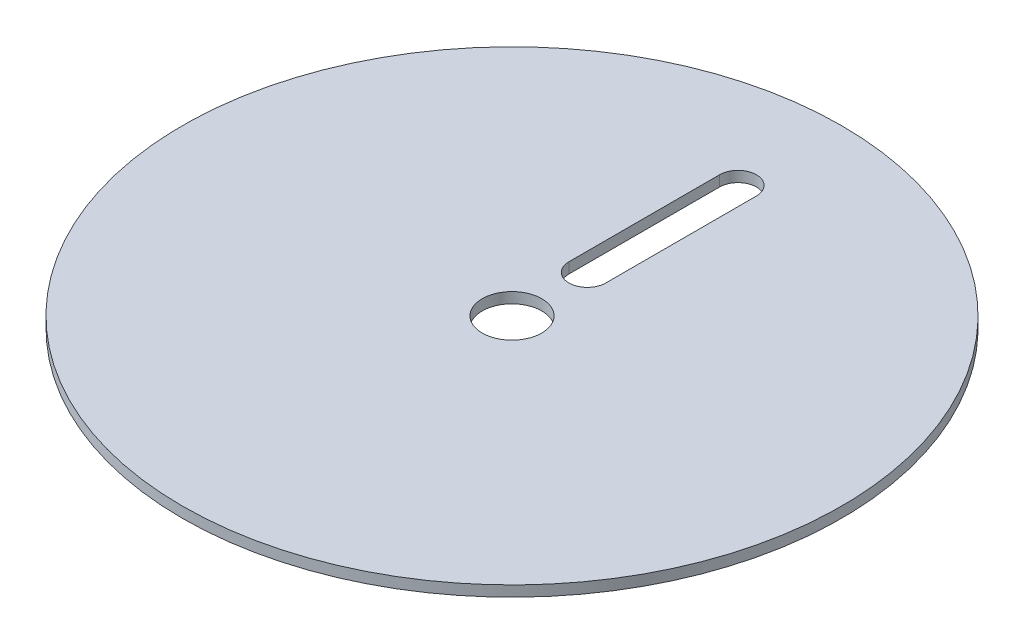
SolidWorks part; units mm, degrees
material "G10 Fiber Reinforced Plastic"
ref_plane "Front Plane" through (0, 0, 0) normal (0, 0, 1) x (1, 0, 0)
ref_plane "Top Plane" through (0, 0, 0) normal (0, 1, 0) x (1, 0, 0)
ref_plane "Right Plane" through (0, 0, 0) normal (1, 0, 0) x (0, 0, -1)
sketch "Sketch1" plane through (0, 0, 0) normal (0, 1, 0) x (1, 0, 0)
  line L0 (0, 0) -> (0, 22.5) construction
  line L2 (0, 22.5) -> (0, 67.5) construction
  line L3 (-5.5, 22.5) -> (-5.5, 67.5)
  line L4 (5.5, 22.5) -> (5.5, 67.5)
  circle A0 centre (0, 0) radius 98.425
  arc A1 (-5.5, 22.5) -> (5.5, 22.5) centre (0, 22.5) ccw
  circle A2 centre (0, 0) radius 8.89
  arc A3 (5.5, 67.5) -> (-5.5, 67.5) centre (0, 67.5) ccw
  point P3 (0, 45)
  dimension "D1" = 196.85
  dimension "D2" = 17.78
  dimension "D3" = 11
  dimension "D4" = 45
  dimension "D5" = 22.5
extrude "Boss-Extrude1" add sketch "Sketch1" along normal blind 3.175
